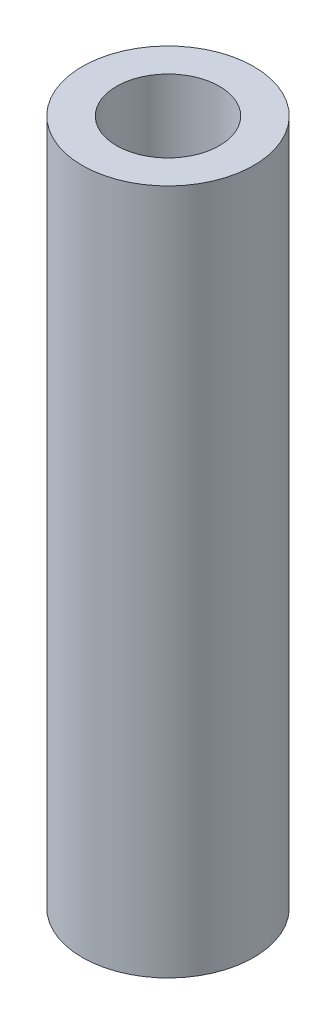
SolidWorks part; units mm, degrees
ref_plane "Front Plane" through (0, 0, 0) normal (0, 0, 1) x (1, 0, 0)
ref_plane "Top Plane" through (0, 0, 0) normal (0, 1, 0) x (1, 0, 0)
ref_plane "Right Plane" through (0, 0, 0) normal (1, 0, 0) x (0, 0, -1)
sketch "Sketch1" plane through (0, 0, 0) normal (0, 1, 0) x (1, 0, 0)
  circle A0 centre (0, 0) radius 2.5
  circle A1 centre (0, 0) radius 1.5
  dimension "D1" = 3
  dimension "D2" = 5
extrude "Boss-Extrude1" add sketch "Sketch1" along normal blind 20
